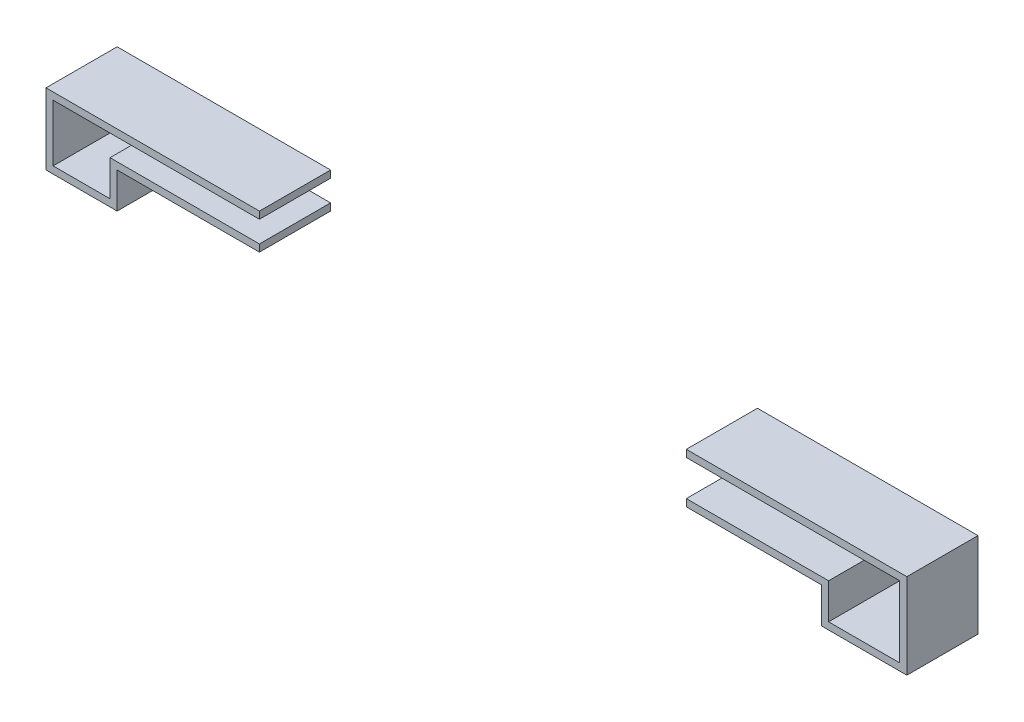
SolidWorks part; units mm, degrees
ref_plane "Front Plane" through (0, 0, 0) normal (0, 0, 1) x (1, 0, 0)
ref_plane "Top Plane" through (0, 0, 0) normal (0, 1, 0) x (1, 0, 0)
ref_plane "Right Plane" through (0, 0, 0) normal (1, 0, 0) x (0, 0, -1)
sketch "Sketch1" plane through (0, 0, 0) normal (0, 1, 0) x (1, 0, 0)
  line L0 (-5, 0) -> (5, 0)
  dimension "D1" = 10
sketch "Sketch2" plane through (0, 0, 0) normal (0, 0, 1) x (1, 0, 0)
  line L0 (-5, 0) -> (-5, 0.5)
  line L1 (-5, 0.5) -> (-3, 0.5)
  line L2 (5, 0) -> (5, 0.5)
  line L3 (5, 0.5) -> (3, 0.5)
  line L4 (6, 0) -> (6, 1)
  line L5 (6, 1) -> (3, 1)
  line L6 (-6, 0) -> (-6, 1)
  line L7 (-6, 1) -> (-3, 1)
  line L8 (-6, 0) -> (-5, 0)
  line L9 (5, 0) -> (6, 0)
  line L11 (-5, 0) -> (5, 0) construction
  point P15 (0, 0)
  point P17 (0, 0)
  point P18 (-4.2872, 0.5)
  point P19 (0, 0)
  point P20 (0, 0)
  dimension "D1" = 1
  dimension "D2" = 1
  dimension "D3" = 2
  dimension "D4" = 3
  dimension "D5" = 0.5
  dimension "D6" = 0.5
extrude "Extrude-Thin2" add sketch "Sketch2" along normal blind 1 thin thin type one direction wall 0.1
